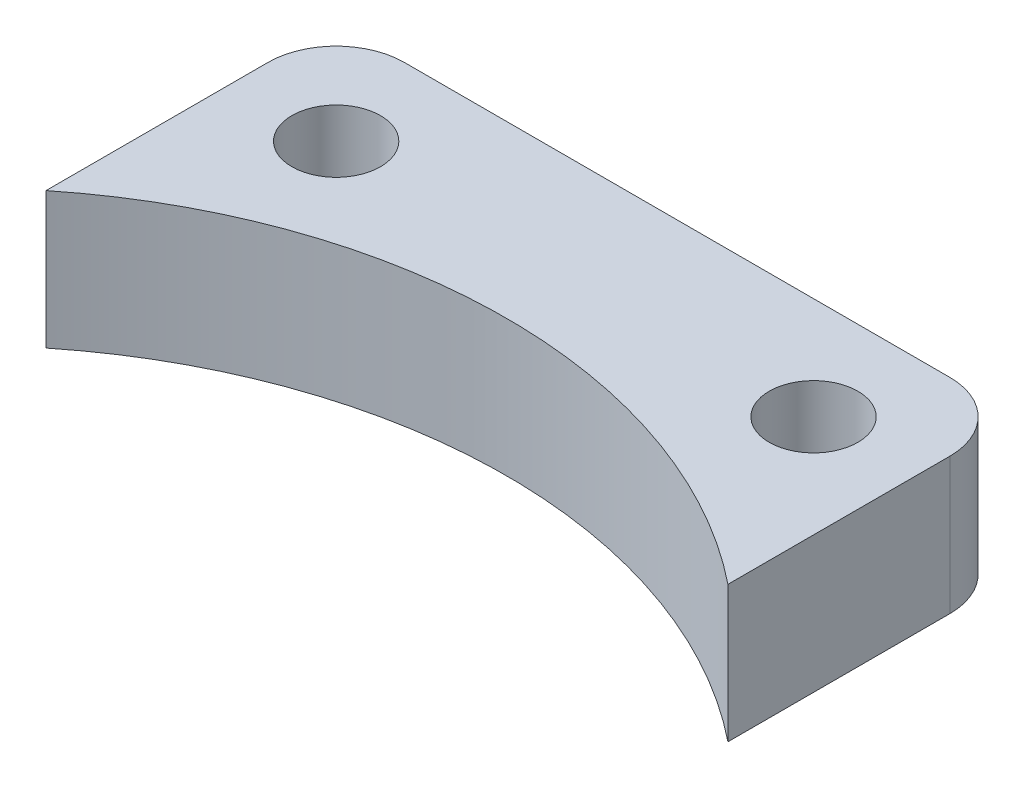
SolidWorks part; units mm, degrees
ref_plane "Plan de face" through (0, 0, 0) normal (0, 0, 1) x (1, 0, 0)
ref_plane "Plan de dessus" through (0, 0, 0) normal (0, 1, 0) x (1, 0, 0)
ref_plane "Plan de droite" through (0, 0, 0) normal (1, 0, 0) x (0, 0, -1)
sketch "Esquisse1" plane through (0, 0, 0) normal (0, 1, 0) x (1, 0, 0)
  line L0 (0, 0) -> (0, 223.7456) construction
  line L1 (25, 31.225) -> (25, 52.5)
  line L2 (-25, 31.225) -> (-25, 52.5)
  line L3 (-25, 52.5) -> (25, 52.5)
  line L9 (25, 0) -> (25, 223.7456) construction
  line L11 (-25, 0) -> (-25, 223.7456) construction
  arc A0 (25, 31.225) -> (-25, 31.225) centre (0, 0) ccw
  dimension "D1" = 40
extrude "Boss.-Extru.1" add sketch "Esquisse1" along normal blind 10
fillet "Congé1" radius 5 2 edges at (25, 5, -52.5) (-25, 5, -52.5)
sketch "Esquisse3" plane through (0, 10, 0) normal (0, 1, 0) x (1, 0, 0)
  circle A0 centre (-17.5, 45) radius 3.25
  circle A1 centre (17.5, 45) radius 3.25
extrude "Enlèv. mat.-Extru.1" cut sketch "Esquisse3" against normal through all
